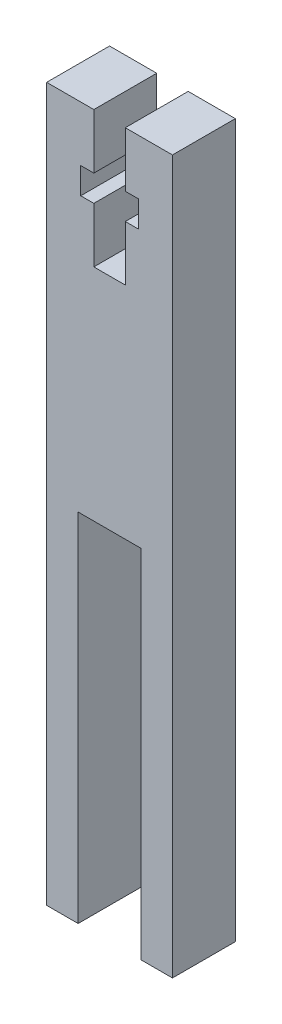
SolidWorks part; units mm, degrees
ref_plane "Спереди" through (0, 0, 0) normal (0, 0, 1) x (1, 0, 0)
ref_plane "Сверху" through (0, 0, 0) normal (0, 1, 0) x (1, 0, 0)
ref_plane "Справа" through (0, 0, 0) normal (1, 0, 0) x (0, 0, -1)
other "Configuration Table"
sketch "Эскиз1" plane through (0, 0, 0) normal (0, 0, 1) x (1, 0, 0)
  line L0 (0, 0) -> (0, 68) construction
  line L1 (0, 34) -> (-21.3565, 34) construction
  line L2 (-1.5, 68) -> (-1.5, 62.75)
  line L3 (-1.5, 62.75) -> (-2.75, 62.75)
  line L4 (-2.75, 62.75) -> (-2.75, 60.25)
  line L5 (-2.75, 60.25) -> (-1.5, 60.25)
  line L6 (-1.5, 60.25) -> (-1.5, 55)
  line L7 (-1.5, 55) -> (1.5, 55)
  line L8 (1.5, 60.25) -> (1.5, 55)
  line L9 (2.75, 60.25) -> (1.5, 60.25)
  line L10 (2.75, 62.75) -> (2.75, 60.25)
  line L11 (1.5, 62.75) -> (2.75, 62.75)
  line L12 (1.5, 68) -> (1.5, 62.75)
  line L25 (-1.5, 68) -> (-6, 68)
  line L26 (-6, 68) -> (-6, 0)
  line L28 (6, 68) -> (6, 0)
  line L29 (1.5, 68) -> (6, 68)
  line L30 (-6, 0) -> (-3, 0)
  line L31 (-3, 0) -> (-3, 34)
  line L32 (-3, 34) -> (3, 34)
  line L33 (3, 0) -> (3, 34)
  line L34 (6, 0) -> (3, 0)
  point P13 (0, 55)
  point P18 (2.75, 61.5)
  point P23 (0, 34)
  dimension "D1" = 2.5
  dimension "D2" = 3
  dimension "D3" = 5.5
  dimension "D4" = 13
  dimension "D5" = 6
  dimension "D6" = 12
  dimension "D7" = 68
extrude "Бобышка-Вытянуть1" add sketch "Эскиз1" along normal blind 6
